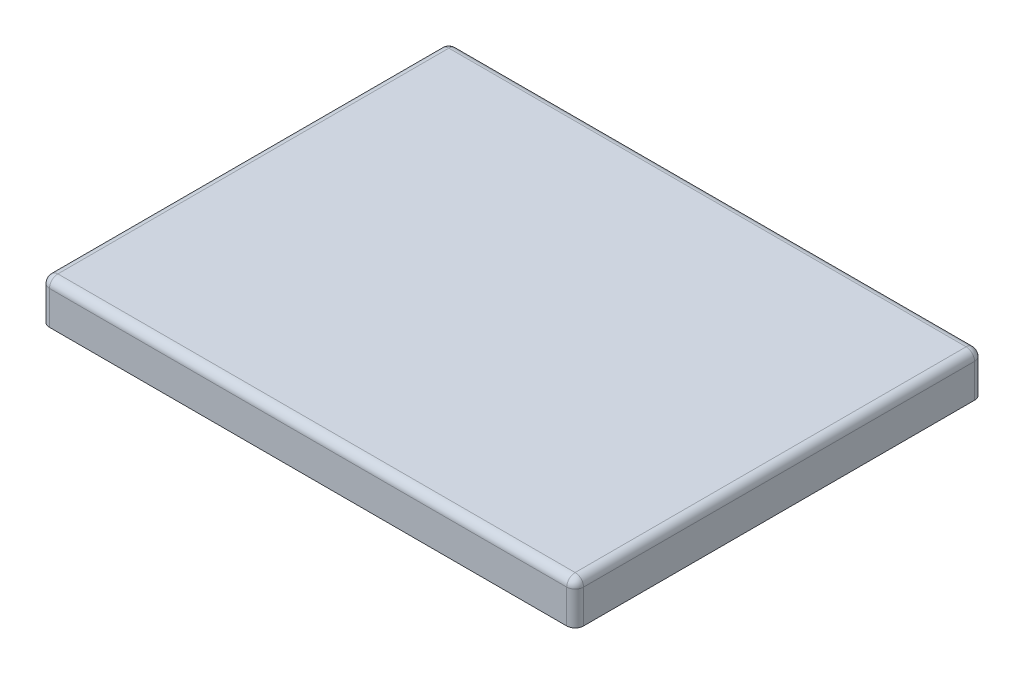
SolidWorks part; units mm, degrees
ref_plane "Front Plane" through (0, 0, 0) normal (0, 0, 1) x (1, 0, 0)
ref_plane "Top Plane" through (0, 0, 0) normal (0, 1, 0) x (1, 0, 0)
ref_plane "Right Plane" through (0, 0, 0) normal (1, 0, 0) x (0, 0, -1)
sketch "Sketch1" plane through (0, 0, 0) normal (0, 1, 0) x (1, 0, 0)
  line L1 (-317.5, 241.3) -> (317.5, 241.3)
  line L2 (-317.5, 241.3) -> (-317.5, -241.3)
  line L3 (-317.5, -241.3) -> (317.5, -241.3)
  line L4 (317.5, 241.3) -> (317.5, -241.3)
  line L5 (-317.5, 241.3) -> (317.5, -241.3) construction
  line L6 (-317.5, -241.3) -> (317.5, 241.3) construction
  line L7 (-322.2625, 246.0625) -> (322.2625, 246.0625)
  line L8 (-322.2625, 246.0625) -> (-322.2625, -246.0625)
  line L9 (-322.2625, -246.0625) -> (322.2625, -246.0625)
  line L10 (322.2625, 246.0625) -> (322.2625, -246.0625)
  line L11 (-322.2625, 246.0625) -> (322.2625, -246.0625) construction
  line L12 (-322.2625, -246.0625) -> (322.2625, 246.0625) construction
  point P0 (0, 0)
  point P6 (0, 0)
  dimension "D1" = 4.7625
  dimension "D2" = 4.7625
  dimension "D3" = 635
  dimension "19" = 482.6
extrude "Boss-Extrude1" add sketch "Sketch1" along normal blind 50.8
sketch "Sketch2" plane through (322.2625, 0, 0) normal (1, 0, 0) x (0, 0, -1)
  line L0 (246.0625, 50.8) -> (246.0625, 0) construction
  line L1 (-246.0625, 50.8) -> (246.0625, 50.8)
  line L2 (-246.0625, 50.8) -> (-246.0625, 46.0375)
  line L3 (-246.0625, 46.0375) -> (246.0625, 46.0375)
  line L4 (246.0625, 50.8) -> (246.0625, 46.0375)
  dimension "D1" = 4.7625
extrude "Boss-Extrude2" add sketch "Sketch2" against normal blind 644.525
fillet "Fillet1" radius 10.16 8 edges at (-322.2625, 25.4, 246.0625) (322.2625, 25.4, 246.0625) (322.2625, 25.4, -246.0625) (-322.2625, 25.4, -246.0625) (-322.2625, 50.8, 0) (0, 50.8, -246.0625) (322.2625, 50.8, 0) (0, 50.8, 246.0625)
